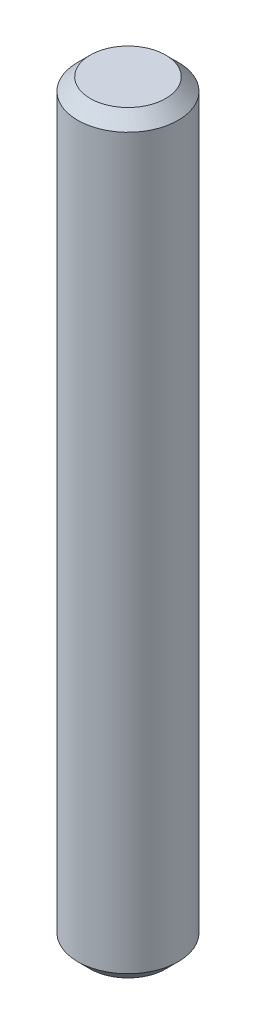
SolidWorks part; units mm, degrees
ref_plane "Front Plane" through (0, 0, 0) normal (0, 0, 1) x (1, 0, 0)
ref_plane "Top Plane" through (0, 0, 0) normal (0, 1, 0) x (1, 0, 0)
ref_plane "Right Plane" through (0, 0, 0) normal (1, 0, 0) x (0, 0, -1)
sketch "Sketch1" plane through (0, 0, 0) normal (0, 1, 0) x (1, 0, 0)
  circle A0 centre (0, 0) radius 2
  dimension "D1" = 4
extrude "Boss-Extrude1" add sketch "Sketch1" along normal mid plane 30
chamfer "Chamfer1" distance 0.5 angle 45 2 edges at (0, -15, 2) (0, 15, 2)
